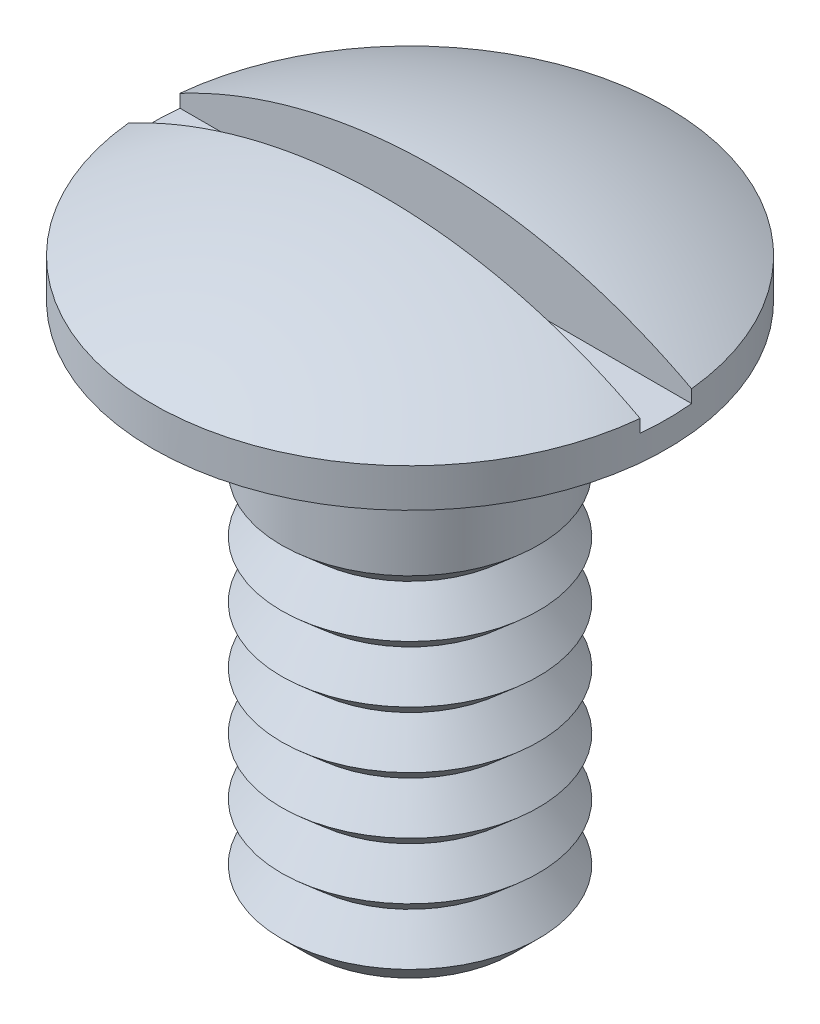
SolidWorks part; units mm, degrees
ref_plane "Plan de face" through (0, 0, 0) normal (0, 0, 1) x (1, 0, 0)
ref_plane "Plan de dessus" through (0, 0, 0) normal (0, 1, 0) x (1, 0, 0)
ref_plane "Plan de droite" through (0, 0, 0) normal (1, 0, 0) x (0, 0, -1)
sketch "Esquisse1" plane through (0, 0, 0) normal (1, 0, 0) x (0, 0, -1)
  line L0 (0, 0) -> (-0.5, 0)
  line L1 (-0.5, 0) -> (-0.5, 2)
  line L2 (-0.5, 2) -> (-1, 2)
  line L3 (-1, 2) -> (-1, 2.15)
  line L4 (0, 0) -> (0, 2.4) construction
  line L5 (0, 2.4) -> (0.5083, 2.4) construction
  line L6 (0, 0) -> (0, 2.4)
  arc A0 (0, 2.4) -> (-1, 2.15) centre (0, 0.275) ccw
  dimension "D1" = 1
  dimension "D2" = 2
  dimension "D3" = 2
  dimension "D4" = 0.15
  dimension "D5" = 0.4
revolve "Révolution1" add sketch "Esquisse1" angle 360 about L6
sketch "Esquisse2" plane through (0, 0, 0) normal (1, 0, 0) x (0, 0, -1)
  line L1 (-0.1, 2.7) -> (0.1, 2.7)
  line L2 (-0.1, 2.7) -> (-0.1, 2.1)
  line L3 (-0.1, 2.1) -> (0.1, 2.1)
  line L4 (0.1, 2.7) -> (0.1, 2.1)
  line L5 (-0.1, 2.7) -> (0.1, 2.1) construction
  line L6 (-0.1, 2.1) -> (0.1, 2.7) construction
  arc A0 (1, 2.15) -> (-1, 2.15) centre (0, 0.275) ccw construction
  point P0 (0, 2.4)
  dimension "D1" = 0.2
  dimension "D2" = 2.1
extrude "Enlèv. mat.-Extru.1" cut sketch "Esquisse2" against normal mid plane 3
chamfer "Chanfrein1" distance 0.1 angle 45 1 edges at (0, 0, -0.5)
sketch "Esquisse3" plane through (0, 0, 0) normal (0, 0, 1) x (1, 0, 0)
  line L0 (-0.5, 0.1) -> (-0.3905, 0.2249)
  line L1 (-0.3905, 0.2249) -> (-0.5, 0.3209)
  line L2 (-0.5, 2) -> (-0.5, 0.1) construction
  line L3 (-0.5, 0.3209) -> (-0.3905, 0.4459)
  line L4 (-0.3905, 0.4459) -> (-0.5, 0.5419)
  line L5 (-0.5, 0.5419) -> (-0.3905, 0.6668)
  line L6 (-0.3905, 0.6668) -> (-0.5, 0.7628)
  line L7 (-0.5, 0.7628) -> (-0.3905, 0.8877)
  line L8 (-0.3905, 0.8877) -> (-0.5, 0.9838)
  line L9 (-0.5, 0.9838) -> (-0.3905, 1.1087)
  line L10 (-0.3905, 1.1087) -> (-0.5, 1.2047)
  line L11 (-0.5, 1.2047) -> (-0.3905, 1.3296)
  line L12 (-0.3905, 1.3296) -> (-0.5, 1.4256)
  line L13 (-0.5, 1.4256) -> (-0.8223, 1.4256)
  line L14 (-0.8223, 1.4256) -> (-0.8223, 0.1)
  line L15 (-0.8223, 0.1) -> (-0.5, 0.1)
revolve "Enlèvement de matière-Révolution1" cut sketch "Esquisse3" angle 360 about axis through (0, 0, 0) along (0, -1, 0)
